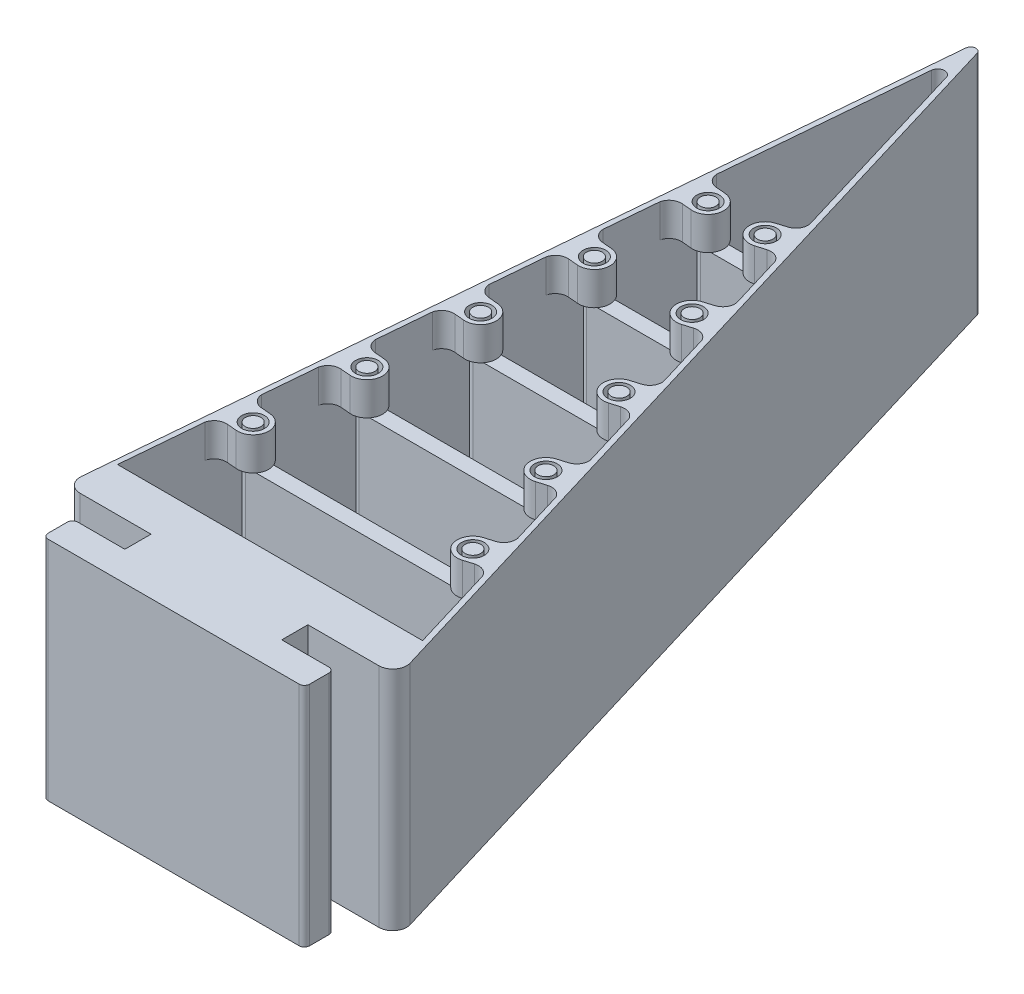
SolidWorks part; units mm, degrees
ref_plane "Front Plane" through (0, 0, 0) normal (0, 0, 1) x (1, 0, 0)
ref_plane "Top Plane" through (0, 0, 0) normal (0, 1, 0) x (1, 0, 0)
ref_plane "Right Plane" through (0, 0, 0) normal (1, 0, 0) x (0, 0, -1)
sketch "Sketch1" plane through (0, 0, 0) normal (0, 1, 0) x (1, 0, 0)
  line L0 (0, 0) -> (7.5114, 85.8562)
  line L1 (9.0744, 86.0173) -> (35, 0)
  line L2 (35, 0) -> (0, 0)
  line L3 (0, 0) -> (0, 120.308) construction
  line L4 (35.8075, -0.6) -> (-0.6548, -0.6) construction
  line L5 (-0.8876, -3.2606) -> (7.2763, 90.0523)
  line L6 (8.4485, 90.1731) -> (36.5123, -2.9383)
  line L7 (7.5482, 93.1602) -> (35.8075, -0.6) construction
  line L8 (-0.6548, -0.6) -> (7.5482, 93.1602) construction
  line L9 (7.874, 90) -> (35, 0) construction
  line L10 (0, 0) -> (7.874, 90) construction
  line L11 (0.7064, -5) -> (34.9803, -5)
  arc A0 (8.4485, 90.1731) -> (7.2763, 90.0523) centre (7.874, 90) ccw
  arc A1 (9.0744, 86.0173) -> (7.5114, 85.8562) centre (8.3084, 85.7864) ccw
  arc A2 (34.9803, -5) -> (36.5123, -2.9383) centre (34.9803, -3.4) ccw
  arc A3 (-0.8876, -3.2606) -> (0.7064, -5) centre (0.7064, -3.4) ccw
  point P14 (7.874, 90)
  dimension "D5" = 0.6
  dimension "D6" = 0.8
  dimension "D8" = 1.6
  dimension "D1" = 90
  dimension "D2" = 5
  dimension "D3" = 35
  dimension "D7" = 5
  dimension "D4" = 0.6
extrude "Boss-Extrude1" add sketch "Sketch1" along normal blind 26
sketch "Sketch3" plane through (0, 26, 0) normal (0, 1, 0) x (1, 0, 0)
  line L0 (5.7558, 49.8903) -> (6.8659, 49.7932)
  line L1 (7.5114, 85.8562) -> (0, 0) construction
  line L2 (5.442, 46.304) -> (6.5521, 46.2068)
  line L3 (6.8056, 61.8903) -> (7.9157, 61.7932)
  line L4 (6.4919, 58.304) -> (7.602, 58.2068)
  line L5 (14.8524, 62.045) -> (13.7855, 61.7234)
  line L6 (15.8913, 58.5982) -> (14.8243, 58.2766)
  line L7 (35, 0) -> (9.0744, 86.0173) construction
  line L8 (18.4692, 50.045) -> (17.4023, 49.7234)
  line L9 (19.5081, 46.5982) -> (18.4411, 46.2766)
  line L10 (23.1249, 34.5982) -> (22.0579, 34.2766)
  line L11 (22.086, 38.045) -> (21.0191, 37.7234)
  line L12 (0, 0) -> (35, 0) construction
  line L13 (3.5594, 12) -> (2.5095, 0) construction
  line L14 (1.1141, -15.9502) -> (14.4036, 135.9502) construction
  line L15 (1.3278, 103.0559) -> (38.7963, -21.2589) construction
  line L16 (36.5123, -2.9383) -> (8.4485, 90.1731) construction
  line L17 (3.5594, 12) -> (4.6093, 24) construction
  line L18 (4.6093, 24) -> (5.6591, 36) construction
  line L19 (6.709, 48) -> (5.6591, 36) construction
  line L20 (7.7589, 60) -> (6.709, 48) construction
  line L21 (2.6062, 13.8903) -> (3.7163, 13.7932)
  line L22 (2.2924, 10.304) -> (3.4025, 10.2068)
  line L23 (3.656, 25.8903) -> (4.7662, 25.7932)
  line L24 (3.3423, 22.304) -> (4.4524, 22.2068)
  line L25 (4.7059, 37.8903) -> (5.816, 37.7932)
  line L26 (4.3921, 34.304) -> (5.5023, 34.2068)
  line L27 (25.7028, 26.045) -> (24.6359, 25.7234)
  line L28 (26.7417, 22.5982) -> (25.6747, 22.2766)
  line L29 (29.3196, 14.045) -> (28.2527, 13.7234)
  line L30 (30.3585, 10.5982) -> (29.2916, 10.2766)
  line L31 (5.5298, 63.2065) -> (5.0069, 57.2293)
  line L32 (4.48, 51.2065) -> (3.9571, 45.2293)
  line L33 (3.4301, 39.2065) -> (2.9072, 33.2293)
  line L34 (2.3803, 27.2065) -> (1.8573, 21.2293)
  line L35 (1.3304, 15.2065) -> (0.8075, 9.2293)
  line L36 (30.3, 15.5938) -> (32.0315, 9.8491)
  line L37 (26.6832, 27.5938) -> (28.4147, 21.8491)
  line L38 (23.0664, 39.5938) -> (24.7979, 33.8491)
  line L39 (19.4496, 51.5938) -> (21.1811, 45.8491)
  line L40 (15.8328, 63.5938) -> (17.5643, 57.8491)
  arc A0 (3.4025, 10.2068) -> (3.7163, 13.7932) centre (3.5594, 12) ccw
  arc A1 (28.2527, 13.7234) -> (29.2916, 10.2766) centre (28.7721, 12) ccw
  arc A2 (4.4524, 22.2068) -> (4.7662, 25.7932) centre (4.6093, 24) ccw
  arc A3 (24.6359, 25.7234) -> (25.6747, 22.2766) centre (25.1553, 24) ccw
  arc A4 (5.5023, 34.2068) -> (5.816, 37.7932) centre (5.6591, 36) ccw
  arc A5 (21.0191, 37.7234) -> (22.0579, 34.2766) centre (21.5385, 36) ccw
  arc A6 (6.5521, 46.2068) -> (6.8659, 49.7932) centre (6.709, 48) ccw
  arc A7 (17.4023, 49.7234) -> (18.4411, 46.2766) centre (17.9217, 48) ccw
  arc A8 (7.602, 58.2068) -> (7.9157, 61.7932) centre (7.7589, 60) ccw
  arc A9 (13.7855, 61.7234) -> (14.8243, 58.2766) centre (14.3049, 60) ccw
  circle A10 centre (7.7589, 60) radius 1.3
  circle A11 centre (14.3049, 60) radius 1.3
  circle A12 centre (17.9217, 48) radius 1.3
  circle A13 centre (21.5385, 36) radius 1.3
  circle A14 centre (25.1553, 24) radius 1.3
  circle A15 centre (28.7721, 12) radius 1.3
  circle A16 centre (3.5594, 12) radius 1.3
  circle A17 centre (4.6093, 24) radius 1.3
  circle A18 centre (5.6591, 36) radius 1.3
  circle A19 centre (6.709, 48) radius 1.3
  arc A20 (32.0315, 9.8491) -> (30.3585, 10.5982) centre (30.7625, 9.2577) ccw
  arc A21 (30.3, 15.5938) -> (29.3196, 14.045) centre (28.9156, 15.3854) cw
  arc A22 (28.4147, 21.8491) -> (26.7417, 22.5982) centre (27.1457, 21.2577) ccw
  arc A23 (26.6832, 27.5938) -> (25.7028, 26.045) centre (25.2988, 27.3854) cw
  arc A24 (24.7979, 33.8491) -> (23.1249, 34.5982) centre (23.5289, 33.2577) ccw
  arc A25 (23.0664, 39.5938) -> (22.086, 38.045) centre (21.682, 39.3854) cw
  arc A26 (21.1811, 45.8491) -> (19.5081, 46.5982) centre (19.9121, 45.2577) ccw
  arc A27 (19.4496, 51.5938) -> (18.4692, 50.045) centre (18.0652, 51.3854) cw
  arc A28 (17.5643, 57.8491) -> (15.8913, 58.5982) centre (16.2953, 57.2577) ccw
  arc A29 (15.8328, 63.5938) -> (14.8524, 62.045) centre (14.4484, 63.3854) cw
  arc A30 (6.8056, 61.8903) -> (5.5298, 63.2065) centre (6.9276, 63.2849) cw
  arc A31 (6.4919, 58.304) -> (5.0069, 57.2293) centre (6.3699, 56.9093) ccw
  arc A32 (4.48, 51.2065) -> (5.7558, 49.8903) centre (5.8778, 51.2849) ccw
  arc A33 (5.442, 46.304) -> (3.9571, 45.2293) centre (5.32, 44.9093) ccw
  arc A34 (3.4301, 39.2065) -> (4.7059, 37.8903) centre (4.8279, 39.2849) ccw
  arc A35 (4.3921, 34.304) -> (2.9072, 33.2293) centre (4.2701, 32.9093) ccw
  arc A36 (2.3803, 27.2065) -> (3.656, 25.8903) centre (3.7781, 27.2849) ccw
  arc A37 (3.3423, 22.304) -> (1.8573, 21.2293) centre (3.2203, 20.9093) ccw
  arc A38 (2.2924, 10.304) -> (0.8075, 9.2293) centre (2.1704, 8.9093) ccw
  arc A39 (2.6062, 13.8903) -> (1.3304, 15.2065) centre (2.7282, 15.2849) cw
  dimension "D1" = 3.6
  dimension "D5" = 2.6
  dimension "D6" = 1.4
  dimension "D2" = 2.5
  dimension "D3" = 2.5
  dimension "D4" = 12
extrude "Boss-Extrude2" add sketch "Sketch3" against normal blind 3.8
ref_plane "Plane1" through (0, 13, 0) normal (0, 1, 0) x (1, 0, 0)
mirror "Mirror1" about plane through (0, 13, 0) normal (0, 1, 0) of "Boss-Extrude2"
ref_plane "Plane2" through (0, 22, 0) normal (0, 1, 0) x (1, 0, 0)
sketch "Sketch4" plane through (0, 22, 0) normal (0, 1, 0) x (1, 0, 0)
  line L0 (3.5594, 12.9) -> (28.7721, 12.9)
  line L1 (3.5594, 11.1) -> (28.7721, 11.1)
  line L2 (-7.5832, 18) -> (44.0859, 18) construction
  line L3 (-7.5832, 30) -> (39.4481, 30) construction
  line L4 (-10.5135, 42) -> (39.4481, 42) construction
  line L5 (-10.5135, 54) -> (41.315, 54) construction
  line L6 (0, 0) -> (35, 0) construction
  line L7 (4.6093, 24.9) -> (25.1553, 24.9)
  line L8 (4.6093, 23.1) -> (25.1553, 23.1)
  line L9 (6.709, 48.9) -> (17.9217, 48.9)
  line L10 (6.709, 47.1) -> (17.9217, 47.1)
  line L11 (5.6591, 36.9) -> (21.5385, 36.9)
  line L12 (5.6591, 35.1) -> (21.5385, 35.1)
  line L13 (7.7589, 60.9) -> (14.3049, 60.9)
  line L14 (7.7589, 59.1) -> (14.3049, 59.1)
  arc A0 (3.5594, 12.9) -> (3.5594, 11.1) centre (3.5594, 12) ccw
  arc A1 (28.7721, 11.1) -> (28.7721, 12.9) centre (28.7721, 12) ccw
  arc A2 (4.6093, 24.9) -> (4.6093, 23.1) centre (4.6093, 24) ccw
  arc A3 (25.1553, 23.1) -> (25.1553, 24.9) centre (25.1553, 24) ccw
  arc A4 (5.6591, 36.9) -> (5.6591, 35.1) centre (5.6591, 36) ccw
  arc A5 (21.5385, 35.1) -> (21.5385, 36.9) centre (21.5385, 36) ccw
  arc A6 (6.709, 48.9) -> (6.709, 47.1) centre (6.709, 48) ccw
  arc A7 (17.9217, 47.1) -> (17.9217, 48.9) centre (17.9217, 48) ccw
  arc A8 (7.7589, 60.9) -> (7.7589, 59.1) centre (7.7589, 60) ccw
  arc A9 (14.3049, 59.1) -> (14.3049, 60.9) centre (14.3049, 60) ccw
  dimension "D1" = 1.8
  dimension "D2" = 18
  dimension "D3" = 12
  dimension "D4" = 12
  dimension "D5" = 12
extrude "Boss-Extrude3" add sketch "Sketch4" against normal blind 18 separate body
sketch "Sketch5" plane through (0, 26, 0) normal (0, 1, 0) x (1, 0, 0)
  circle A0 centre (7.7589, 60) radius 0.9
  circle A1 centre (14.3049, 60) radius 0.9
  circle A2 centre (6.709, 48) radius 0.9
  circle A3 centre (17.9217, 48) radius 0.9
  circle A4 centre (5.6591, 36) radius 0.9
  circle A5 centre (21.5385, 36) radius 0.9
  circle A6 centre (4.6093, 24) radius 0.9
  circle A7 centre (3.5594, 12) radius 0.9
  circle A8 centre (28.7721, 12) radius 0.9
  circle A9 centre (25.1553, 24) radius 0.9
  arc A10 (4.6093, 24.9) -> (4.6093, 23.1) centre (4.6093, 24) ccw construction
extrude "Boss-Extrude4" add sketch "Sketch5" against normal up to surface (4 mm away) up to face at (13.5988, 22, -36)
sketch "Sketch6" plane through (0, 0, 0) normal (0, -1, 0) x (1, 0, 0)
  circle A0 centre (5.6591, -36) radius 0.9
  circle A1 centre (21.5385, -36) radius 0.9
  circle A2 centre (25.1553, -24) radius 0.9
  circle A3 centre (4.6093, -24) radius 0.9
  circle A4 centre (3.5594, -12) radius 0.9
  circle A5 centre (28.7721, -12) radius 0.9
  circle A6 centre (6.709, -48) radius 0.9
  circle A7 centre (17.9217, -48) radius 0.9
  circle A8 centre (14.3049, -60) radius 0.9
  circle A9 centre (7.7589, -60) radius 0.9
  arc A10 (3.5594, -11.1) -> (3.5594, -12.9) centre (3.5594, -12) ccw construction
extrude "Boss-Extrude5" add sketch "Sketch6" against normal up to surface (4 mm away) up to face at (16.1658, 4, -12)
sketch "Sketch7" plane through (0, 26, 0) normal (0, 1, 0) x (1, 0, 0)
  line L0 (26.8433, -5) -> (26.8433, -8)
  line L1 (0.7064, -5) -> (34.9803, -5) construction
  line L2 (8.8433, -8) -> (3.4433, -8)
  line L3 (2.8433, -8.6) -> (2.8433, -10.8)
  line L4 (3.4433, -11.4) -> (32.2433, -11.4)
  line L5 (32.8433, -10.8) -> (32.8433, -8.6)
  line L6 (32.2433, -8) -> (26.8433, -8)
  line L7 (8.8433, -8) -> (8.8433, -5)
  line L8 (8.8433, -5) -> (26.8433, -5)
  arc A0 (32.8433, -10.8) -> (32.2433, -11.4) centre (32.2433, -10.8) cw
  arc A1 (32.8433, -8.6) -> (32.2433, -8) centre (32.2433, -8.6) ccw
  arc A2 (2.8433, -10.8) -> (3.4433, -11.4) centre (3.4433, -10.8) ccw
  arc A3 (3.4433, -8) -> (2.8433, -8.6) centre (3.4433, -8.6) ccw
  point P5 (17.8433, -5)
  point P12 (17.8433, -11.4)
  point P13 (17.8433, -5)
  point P16 (32.8433, -11.4)
  point P19 (32.8433, -8)
  point P22 (2.8433, -11.4)
  point P25 (2.8433, -8)
  dimension "D5" = 0.6
  dimension "D1" = 6
  dimension "D2" = 3
  dimension "D3" = 3.4
  dimension "D4" = 30
extrude "Boss-Extrude6" add sketch "Sketch7" against normal up to surface (26 mm away) up to face at (14.5203, 0, -27.2958)
